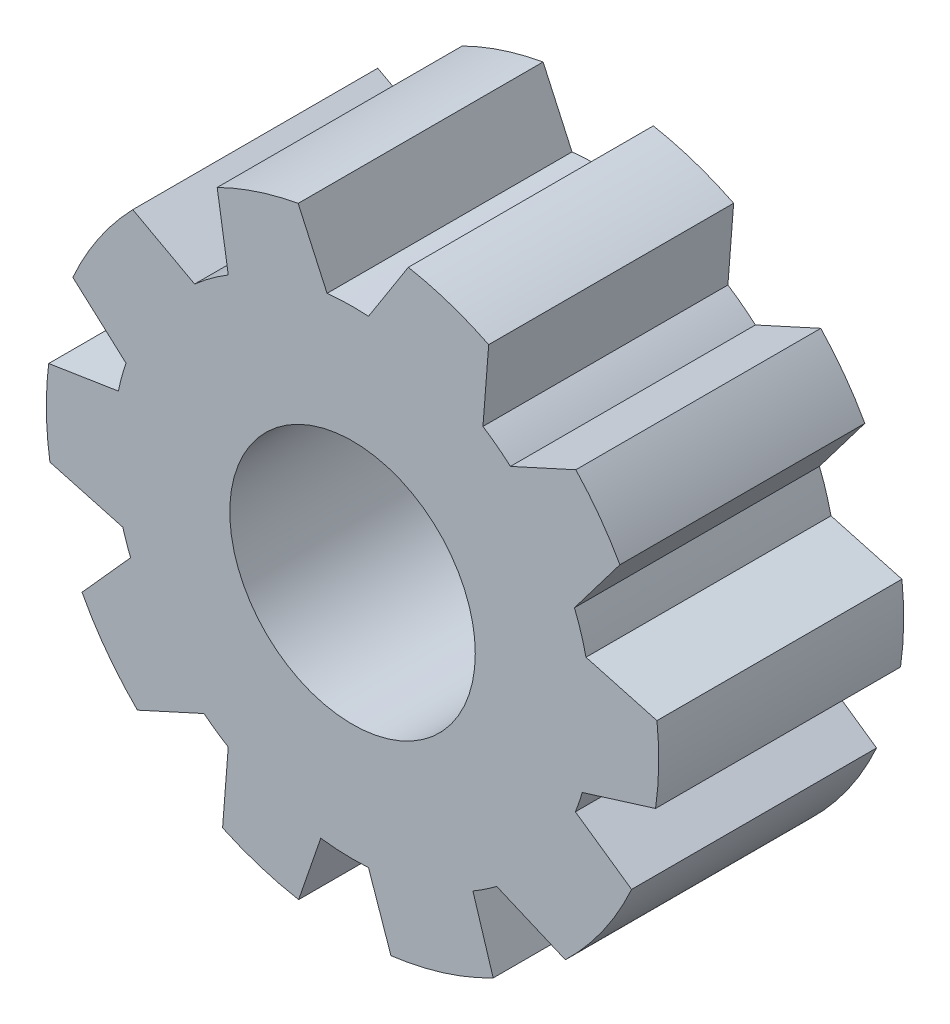
SolidWorks part; units mm, degrees
ref_plane "Front Plane" through (0, 0, 0) normal (0, 0, 1) x (1, 0, 0)
ref_plane "Top Plane" through (0, 0, 0) normal (0, 1, 0) x (1, 0, 0)
ref_plane "Right Plane" through (0, 0, 0) normal (1, 0, 0) x (0, 0, -1)
sketch "Sketch1" plane through (0, 0, 0) normal (0, 0, 1) x (1, 0, 0)
  circle A0 centre (0, 0) radius 6.35
extrude "Boss-Extrude1" add sketch "Sketch1" along normal blind 5.08 contours A0
sketch "Sketch2" plane through (0, 0, 5.08) normal (0, 0, 1) x (1, 0, 0)
  circle A0 centre (0, 0) radius 2.5457
extrude "Cut-Extrude1" cut sketch "Sketch2" against normal blind 5.08
sketch "Sketch6" plane through (0, 0, 0) normal (0, 0, -1) x (-1, 0, 0)
  line L0 (0, 0) -> (-7.1881, 0)
  line L1 (0, 0) -> (-5.6415, -4.0988)
  line L2 (0, 0) -> (-2.1223, -6.5317)
  line L3 (0, 0) -> (2.0812, -6.4054)
  line L4 (0, 0) -> (5.6069, -4.0736)
  line L5 (0, 0) -> (7.3519, 0)
  line L6 (0, 0) -> (-5.9401, 4.3157)
  line L7 (0, 0) -> (-2.1569, 6.6383)
  line L8 (0, 0) -> (2.1034, 6.4737)
  line L9 (0, 0) -> (6.4289, 4.6709)
  line L10 (-6.6219, 0) -> (-6.6219, 0.5964)
  line L11 (-6.6219, 0.5964) -> (-4.8417, 1.0826)
  line L12 (-4.8417, 1.0826) -> (-4.6025, 1.8523)
  line L13 (-4.6025, 1.8523) -> (-5.9401, 3.6164)
  line L14 (-5.9401, 3.6164) -> (-5.0951, 4.556)
  line L15 (-5.0951, 4.556) -> (-3.2749, 3.7269)
  line L16 (-3.2749, 3.7269) -> (-2.7046, 4.1593)
  line L17 (-2.7046, 4.1593) -> (-2.8636, 6.2003)
  line L18 (-2.8636, 6.2003) -> (-1.3873, 6.6035)
  line L19 (-1.3873, 6.6035) -> (-0.3306, 4.9502)
  line L20 (-0.3306, 4.9502) -> (0.5282, 4.9331)
  line L21 (0.5282, 4.9331) -> (1.2891, 6.6035)
  line L22 (1.2891, 6.6035) -> (2.8719, 6.1116)
  line L23 (2.8719, 6.1116) -> (2.5774, 4.2393)
  line L24 (2.5774, 4.2393) -> (3.2749, 3.7269)
  line L25 (3.2749, 3.7269) -> (4.804, 4.556)
  line L26 (4.804, 4.556) -> (5.9683, 2.7344)
  line L27 (5.9683, 2.7344) -> (4.6977, 1.5954)
  line L28 (4.6977, 1.5954) -> (4.8566, 1.014)
  line L29 (4.8566, 1.014) -> (6.6123, 0.7378)
  line L30 (6.6123, 0.7378) -> (6.6123, -0.8801)
  line L31 (6.6123, -0.8801) -> (4.7641, -1.3849)
  line L32 (4.7641, -1.3849) -> (4.6025, -1.8523)
  line L33 (4.6025, -1.8523) -> (5.9683, -3.3759)
  line L34 (5.9683, -3.3759) -> (4.9613, -4.7466)
  line L35 (4.9613, -4.7466) -> (3.0798, -3.8896)
  line L36 (3.0798, -3.8896) -> (2.5774, -4.2393)
  line L37 (2.5774, -4.2393) -> (2.7133, -5.9841)
  line L38 (2.7133, -5.9841) -> (1.1708, -6.4054)
  line L39 (1.1708, -6.4054) -> (0.659, -4.9173)
  line L40 (0.659, -4.9173) -> (-0.3306, -4.9502)
  line L41 (-0.3306, -4.9502) -> (-0.8772, -6.5317)
  line L42 (-0.8772, -6.5317) -> (-2.9897, -5.8752)
  line L43 (-2.9897, -5.8752) -> (-2.4963, -4.2875)
  line L44 (-2.4963, -4.2875) -> (-2.9897, -3.9593)
  line L45 (-2.9897, -3.9593) -> (-4.8417, -4.7466)
  line L46 (-4.8417, -4.7466) -> (-5.9401, -2.7208)
  line L47 (-5.9401, -2.7208) -> (-4.6219, -1.8034)
  line L48 (-4.6219, -1.8034) -> (-4.7641, -1.3849)
  line L49 (-4.7641, -1.3849) -> (-6.6219, -0.8076)
  line L50 (-6.6219, -0.8076) -> (-6.6219, 0)
  circle A0 centre (0, 0) radius 4.9613
  circle A1 centre (0, 0) radius 8.3918
extrude "Cut-Extrude4" cut sketch "Sketch6" against normal blind 5.08
